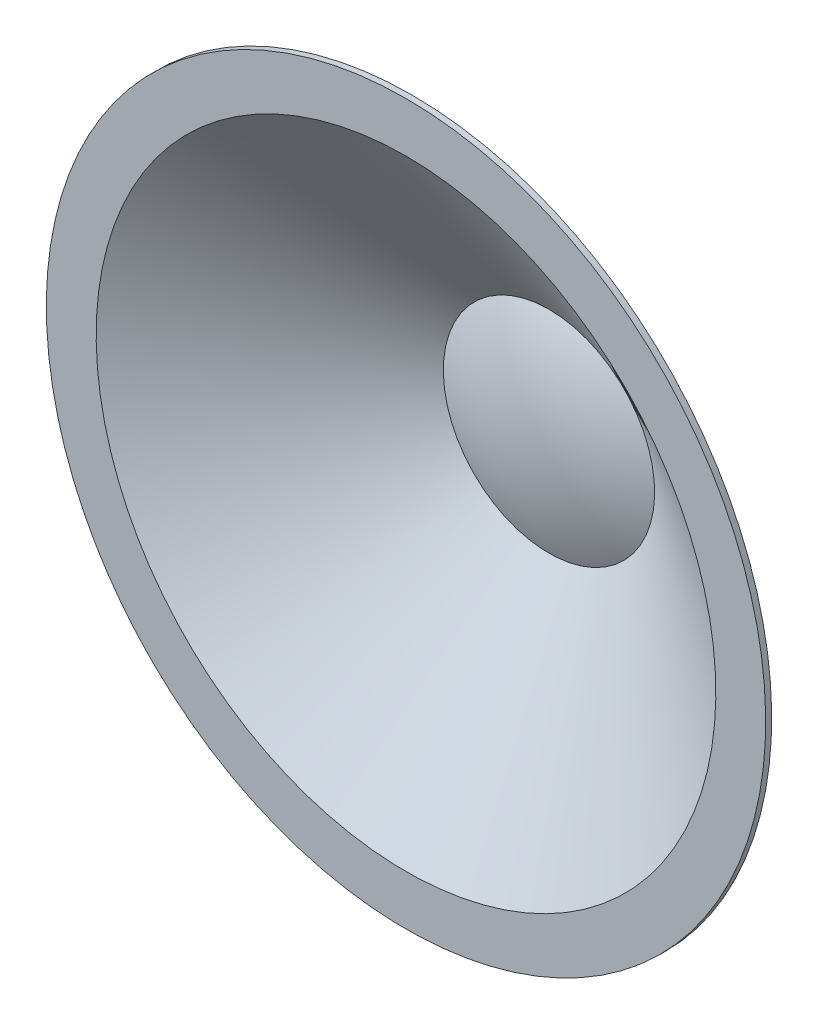
SolidWorks part; units mm, degrees
material "PP Copolymer"
ref_plane "Front" through (0, 0, 0) normal (0, 0, 1) x (1, 0, 0)
ref_plane "Top" through (0, 0, 0) normal (0, 1, 0) x (1, 0, 0)
ref_plane "Right" through (0, 0, 0) normal (1, 0, 0) x (0, 0, -1)
sketch "Sketch1" plane through (0, 0, 0) normal (1, 0, 0) x (0, 0, -1)
  line L0 (0, 30) -> (0, 26)
  line L1 (0, 26) -> (12, 8.8622)
  line L2 (12, 8.8622) -> (12, 0) construction
  line L3 (12, 0) -> (0, 0) construction
  line L4 (10, 0) -> (10, -2.3819) construction
  arc A0 (12, 8.8622) -> (10, 0) centre (30.6348, 0) ccw
  dimension "D1" = 30
  dimension "D2" = 145
  dimension "D3" = 12
  dimension "D4" = 4
  dimension "D5" = 2
revolve "Revolve-Thin1" add sketch "Sketch1" angle 360 about L3
